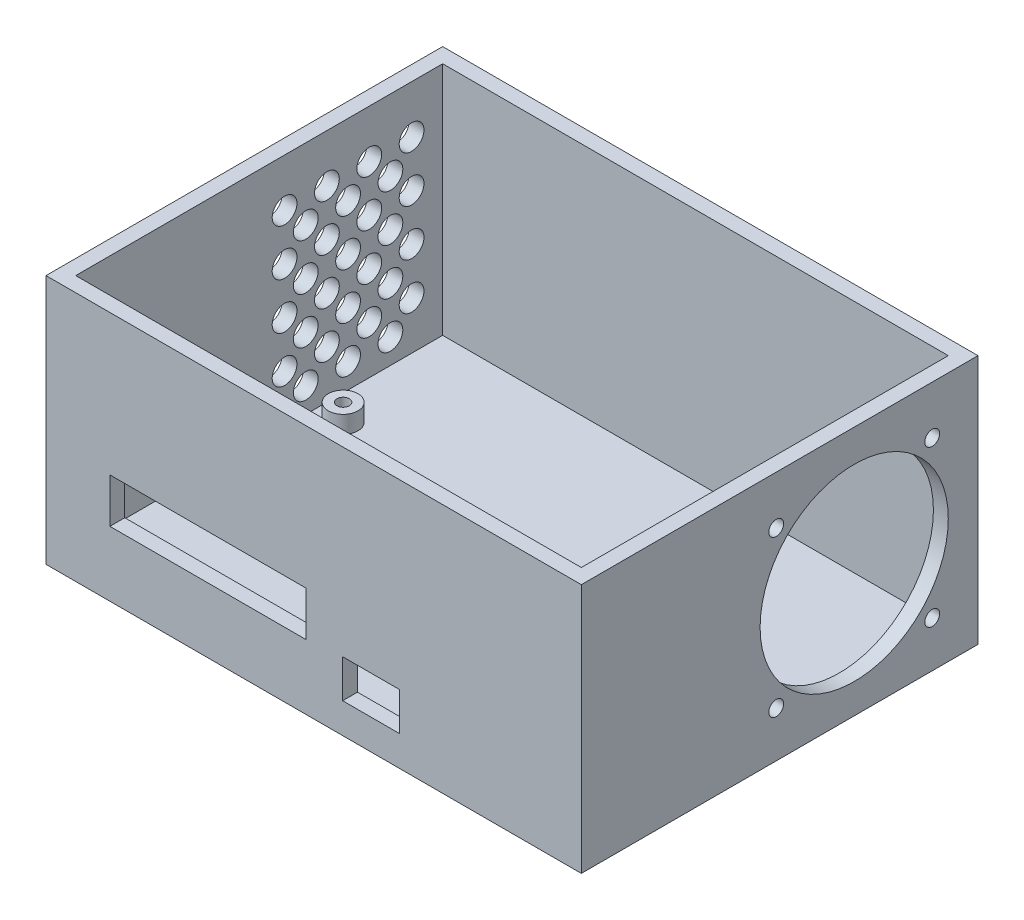
SolidWorks part; units mm, degrees
ref_plane "Front Plane" through (0, 0, 0) normal (0, 0, 1) x (1, 0, 0)
ref_plane "Top Plane" through (0, 0, 0) normal (0, 1, 0) x (1, 0, 0)
ref_plane "Right Plane" through (0, 0, 0) normal (1, 0, 0) x (0, 0, -1)
sketch "Sketch1" plane through (0, 0, 0) normal (0, 1, 0) x (1, 0, 0)
  line L1 (-39.05, -27.95) -> (39.05, -27.95)
  line L2 (-39.05, -27.95) -> (-39.05, 27.95)
  line L3 (-39.05, 27.95) -> (39.05, 27.95)
  line L4 (39.05, -27.95) -> (39.05, 27.95)
  line L5 (-39.05, -27.95) -> (39.05, 27.95) construction
  line L6 (-39.05, 27.95) -> (39.05, -27.95) construction
  point P0 (0, 0)
extrude "Boss-Extrude1" add sketch "Sketch1" along normal blind 3
sketch "Sketch2" plane through (0, 3, 0) normal (0, 1, 0) x (1, 0, 0)
  circle A0 centre (-35.9, 20.9) radius 1.25
  circle A1 centre (-35.9, -24.8) radius 1.25
  circle A2 centre (35.9, -24.8) radius 1.25
  circle A3 centre (35.9, 24.8) radius 1.25
extrude "Cut-Extrude1" cut sketch "Sketch2" against normal blind 68
sketch "Sketch3" plane through (0, 3, 0) normal (0, 1, 0) x (1, 0, 0)
  line L0 (-39.05, -27.95) -> (39.05, -27.95) construction
  line L5 (-31.15, -27.95) -> (8.45, -27.95)
  line L6 (-31.15, -27.95) -> (-31.15, -12.75)
  line L7 (-31.15, -12.75) -> (8.45, -12.75)
  line L8 (8.45, -27.95) -> (8.45, -12.75)
  line L13 (27.35, -17.65) -> (15.85, -17.65)
  line L14 (27.35, -17.65) -> (27.35, -27.95)
  line L15 (27.35, -27.95) -> (15.85, -27.95)
  line L16 (15.85, -17.65) -> (15.85, -27.95)
  line L18 (-39.05, 27.95) -> (39.05, 27.95)
  line L19 (-39.05, 27.95) -> (-39.05, -27.95)
  line L20 (-39.05, -27.95) -> (39.05, -27.95)
  line L21 (39.05, 27.95) -> (39.05, -27.95)
  circle A0 centre (35.9, 24.8) radius 1.25
  circle A1 centre (35.9, -24.8) radius 1.25
  circle A2 centre (-35.9, -24.8) radius 1.25
  circle A3 centre (-35.9, 20.9) radius 1.25
sketch "Sketch4" plane through (0, 0, 0) normal (0, -1, 0) x (-1, 0, 0)
  line L0 (0, -27.95) -> (0, -29.95) construction
  line L1 (39.05, 27.95) -> (-39.05, 27.95)
  line L2 (39.05, 27.95) -> (39.05, -27.95)
  line L3 (39.05, -27.95) -> (-39.05, -27.95)
  line L4 (-39.05, 27.95) -> (-39.05, -27.95)
  line L5 (39.05, 27.95) -> (-39.05, -27.95) construction
  line L6 (39.05, -27.95) -> (-39.05, 27.95) construction
  line L7 (41.05, 29.95) -> (-41.05, 29.95)
  line L8 (41.05, 29.95) -> (41.05, -29.95)
  line L9 (41.05, -29.95) -> (-41.05, -29.95)
  line L10 (-41.05, 29.95) -> (-41.05, -29.95)
  line L11 (41.05, 29.95) -> (-41.05, -29.95) construction
  line L12 (41.05, -29.95) -> (-41.05, 29.95) construction
  line L13 (-39.05, 0) -> (-41.05, 0) construction
  point P0 (0, 0)
  point P7 (0, 0)
extrude "Boss-Extrude3" add sketch "Sketch4" against normal blind 3
sketch "Sketch6" plane through (0, 3, 0) normal (0, 1, 0) x (1, 0, 0)
  circle A0 centre (-35.9, -24.8) radius 1.25
  circle A1 centre (35.9, -24.8) radius 1.25
  circle A2 centre (35.9, 24.8) radius 1.25
  circle A3 centre (-35.9, 20.9) radius 1.25
  circle A4 centre (-35.9, 20.9) radius 3
  circle A5 centre (35.9, 24.8) radius 3
  circle A6 centre (35.9, -24.8) radius 3
  circle A7 centre (-35.9, -24.8) radius 3
extrude "Boss-Extrude4" add sketch "Sketch6" along normal blind 3.5
sketch "Sketch7" plane through (0, 0, 0) normal (0, -1, 0) x (-1, 0, 0)
  line L1 (-41.05, 29.95) -> (41.05, 29.95)
  line L2 (-41.05, 29.95) -> (-41.05, 46.15)
  line L3 (-41.05, 46.15) -> (41.05, 46.15)
  line L4 (41.05, 29.95) -> (41.05, 46.15)
extrude "Boss-Extrude5" add sketch "Sketch7" against normal blind 3
sketch "Sketch8" plane through (0, 0, -46.15) normal (0, 0, -1) x (-1, 0, 0)
  line L1 (-41.05, 0) -> (41.05, 0)
  line L2 (-41.05, 0) -> (-41.05, 50.5)
  line L3 (-41.05, 50.5) -> (41.05, 50.5)
  line L4 (41.05, 0) -> (41.05, 50.5)
extrude "Boss-Extrude6" add sketch "Sketch8" along normal blind 3
sketch "Sketch10" plane through (41.05, 0, 0) normal (1, 0, 0) x (0, 0, -1)
  line L1 (46.15, 50.5) -> (49.15, 50.5)
  line L2 (46.15, 50.5) -> (46.15, 0)
  line L3 (46.15, 0) -> (49.15, 0)
  line L4 (49.15, 50.5) -> (49.15, 0)
  line L5 (-29.95, 0) -> (46.15, 0)
  line L6 (-29.95, 0) -> (-29.95, 3)
  line L7 (-29.95, 3) -> (46.15, 3)
  line L8 (46.15, 0) -> (46.15, 3)
  line M1 (-29.95, 0) -> (49.15, 0)
  line M5 (46.15, 3) -> (-29.95, 3)
  line M6 (-29.95, 3) -> (-29.95, 0)
extrude "Boss-Extrude7" add sketch "Sketch10" along normal blind 20 contours L2 M5 M6 M1
sketch "Sketch12" plane through (-41.05, 0, 0) normal (-1, 0, 0) x (0, 0, 1)
  line L1 (-49.15, 50.5) -> (29.95, 50.5)
  line L2 (-49.15, 50.5) -> (-49.15, 0)
  line L3 (-49.15, 0) -> (29.95, 0)
  line L4 (29.95, 50.5) -> (29.95, 0)
extrude "Boss-Extrude8" add sketch "Sketch12" along normal blind 3
sketch "Sketch17" plane through (0, 0, 29.95) normal (0, 0, 1) x (1, 0, 0)
  line L1 (-44.05, 50.5) -> (61.05, 50.5)
  line L2 (-44.05, 50.5) -> (-44.05, 0)
  line L3 (-44.05, 0) -> (61.05, 0)
  line L4 (61.05, 50.5) -> (61.05, 0)
extrude "Boss-Extrude13" add sketch "Sketch17" against normal blind 2 and the other way blind 1
sketch "Sketch18" plane through (0, 0, 27.95) normal (0, 0, -1) x (-1, 0, 0)
  line L0 (-61.05, 3) -> (-61.05, 50.5) construction
  line L1 (41.05, 3) -> (-61.05, 3)
  line L2 (41.05, 3) -> (41.05, 6.5)
  line L4 (-61.05, 3) -> (-61.05, 6.5)
  line L10 (-8.45, 8.1) -> (-8.45, 13.1) construction
  line L19 (-8.45, 8.1) -> (-8.45, 22.1) construction
  line L21 (-8.45, 22.1) -> (31.15, 22.1)
  line L22 (-8.45, 22.1) -> (-8.45, 13.1)
  line L23 (-8.45, 13.1) -> (31.15, 13.1)
  line L24 (31.15, 22.1) -> (31.15, 13.1)
  line L31 (-25.35, 8.1) -> (-17.85, 11.8) construction
  line L32 (-25.35, 11.8) -> (-17.85, 8.1) construction
  line L38 (-27.35, 6.1) -> (-15.85, 6.1)
  line L39 (-27.35, 6.1) -> (-27.35, 13.8)
  line L40 (-27.35, 13.8) -> (-15.85, 13.8)
  line L41 (-15.85, 6.1) -> (-15.85, 13.8)
  line L42 (-27.35, 6.1) -> (-15.85, 13.8) construction
  line L43 (-27.35, 13.8) -> (-15.85, 6.1) construction
  point P7 (-21.6, 9.95)
  point P8 (-21.6, 9.95)
  point P27 (-21.6, 9.95)
  point P32 (-21.6, 9.95)
extrude "Cut-Extrude4" cut sketch "Sketch18" against normal blind 9 contours L38 L41 L40 L39 | L24 L21 L22 L23
sketch "Sketch19" plane through (61.05, 0, 0) normal (1, 0, 0) x (0, 0, -1)
  line L1 (-30.95, 50.5) -> (49.15, 50.5)
  line L2 (-30.95, 50.5) -> (-30.95, 0)
  line L3 (-30.95, 0) -> (49.15, 0)
  line L4 (49.15, 50.5) -> (49.15, 0)
extrude "Boss-Extrude14" add sketch "Sketch19" along normal blind 3
sketch "Sketch20" plane through (61.05, 0, 0) normal (-1, 0, 0) x (0, 0, 1)
  line L0 (-34.985, 3) -> (-34.985, 5) construction
  line L1 (-46.15, 3) -> (27.95, 3) construction
  line L2 (-46.15, 21.4946) -> (-44.15, 21.4946) construction
  line L3 (-46.15, 50.5) -> (-46.15, 3) construction
  line L4 (-44.15, 45) -> (-4.15, 5) construction
  line L14 (-39.9, 9.25) -> (-8.4, 40.75) construction
  line L15 (-39.9, 40.75) -> (-8.4, 9.25) construction
  circle A0 centre (-24.15, 25) radius 19
  circle A1 centre (-8.4, 40.75) radius 1.5
  circle A2 centre (-39.9, 40.75) radius 1.5
  circle A3 centre (-8.4, 9.25) radius 1.5
  circle A4 centre (-39.9, 9.25) radius 1.5
extrude "Cut-Extrude5" cut sketch "Sketch20" against normal blind 3
sketch "Sketch22" plane through (-41.05, 0, 0) normal (1, 0, 0) x (0, 0, -1)
  line L0 (46.15, 3) -> (27.95, 3) construction
  line L1 (-27.95, 3) -> (46.15, 3) construction
  line L2 (27.95, 3) -> (9.95, 3) construction
  line L3 (46.15, 26.75) -> (44.15, 26.75) construction
  line L4 (46.15, 3) -> (46.15, 50.5) construction
  line L5 (9.95, 45.5) -> (9.95, 36.125) construction
  line L6 (-27.95, 50.5) -> (46.15, 50.5) construction
  line L7 (44.15, 3) -> (44.15, 50.5) construction
  line L8 (18.5, 50.5) -> (18.5, 3) construction
  line L9 (9.95, 50.5) -> (18.5, 50.5) construction
  line L10 (27.05, 50.5) -> (27.05, 3) construction
  line L11 (18.5, 50.5) -> (27.05, 50.5) construction
  line L12 (35.6, 50.5) -> (35.6, 3) construction
  line L13 (27.05, 50.5) -> (35.6, 50.5) construction
  line L14 (35.6, 50.5) -> (44.15, 50.5) construction
  line L15 (14.225, 50.5) -> (14.225, 3) construction
  line L16 (22.775, 50.5) -> (22.775, 3) construction
  line L17 (31.325, 50.5) -> (31.325, 3) construction
  line L18 (39.875, 50.5) -> (39.875, 3) construction
  line L19 (9.95, 26.75) -> (44.15, 26.75) construction
  line L20 (9.95, 36.125) -> (9.95, 26.75) construction
  line L21 (9.95, 45.5) -> (44.15, 45.5) construction
  line L22 (9.95, 8) -> (44.15, 8) construction
  line L23 (9.95, 17.375) -> (44.15, 17.375) construction
  line L24 (9.95, 36.125) -> (44.15, 36.125) construction
  line L25 (9.95, 26.75) -> (9.95, 17.375) construction
  line L26 (9.95, 17.375) -> (9.95, 8) construction
  line L27 (9.95, 40.8125) -> (44.15, 40.8125) construction
  line L28 (9.95, 31.4375) -> (44.15, 31.4375) construction
  line L29 (9.95, 22.0625) -> (44.15, 22.0625) construction
  line L30 (9.95, 12.6875) -> (44.15, 12.6875) construction
  circle A0 centre (14.225, 12.6875) radius 2.5
  circle A1 centre (14.225, 22.0625) radius 2.5
  circle A2 centre (18.5, 17.375) radius 2.5
  circle A3 centre (22.775, 22.0625) radius 2.5
  circle A4 centre (22.775, 12.6875) radius 2.5
  circle A5 centre (14.225, 31.4375) radius 2.5
  circle A6 centre (18.5, 26.75) radius 2.5
  circle A7 centre (22.775, 31.4375) radius 2.5
  circle A8 centre (18.5, 36.125) radius 2.5
  circle A9 centre (14.225, 40.8125) radius 2.5
  circle A10 centre (22.775, 40.8125) radius 2.5
  circle A11 centre (27.05, 36.125) radius 2.5
  circle A12 centre (31.325, 40.8125) radius 2.5
  circle A13 centre (39.875, 40.8125) radius 2.5
  circle A14 centre (35.6, 36.125) radius 2.5
  circle A15 centre (39.875, 31.4375) radius 2.5
  circle A16 centre (31.325, 31.4375) radius 2.5
  circle A17 centre (27.05, 26.75) radius 2.5
  circle A18 centre (31.325, 22.0625) radius 2.5
  circle A19 centre (39.875, 22.0625) radius 2.5
  circle A20 centre (35.6, 26.75) radius 2.5
  circle A21 centre (27.05, 17.375) radius 2.5
  circle A22 centre (31.325, 12.6875) radius 2.5
  circle A23 centre (39.875, 12.6875) radius 2.5
  circle A24 centre (35.6, 17.375) radius 2.5
  circle A26 centre (18.5, 8) radius 2.5
  circle A27 centre (27.05, 8) radius 2.5
  circle A28 centre (35.6, 8) radius 2.5
extrude "Cut-Extrude6" cut sketch "Sketch22" against normal blind 3
